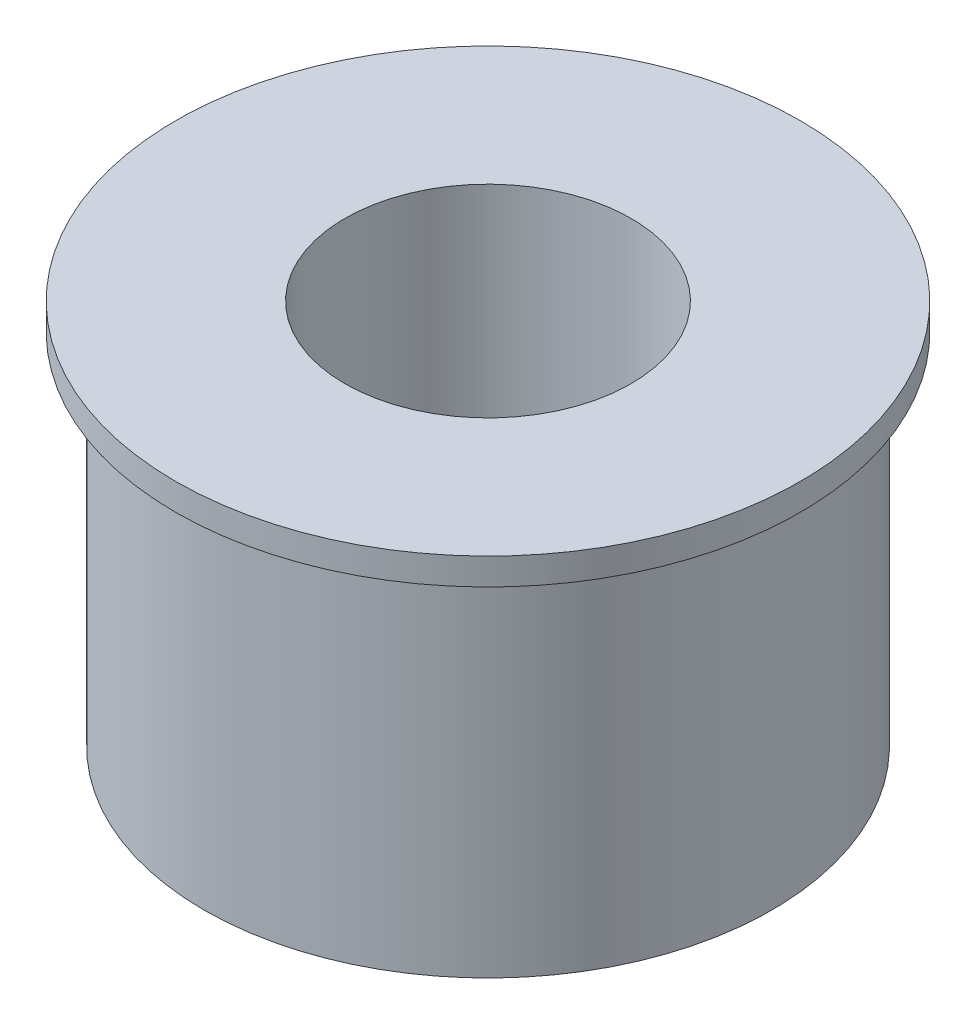
SolidWorks part; units mm, degrees
material "Aluminum Bronze"
ref_plane "Front Plane" through (0, 0, 0) normal (0, 0, 1) x (1, 0, 0)
ref_plane "Top Plane" through (0, 0, 0) normal (0, 1, 0) x (1, 0, 0)
ref_plane "Right Plane" through (0, 0, 0) normal (1, 0, 0) x (0, 0, -1)
sketch "Sketch1" plane through (0, 0, 0) normal (0, 1, 0) x (1, 0, 0)
  circle A0 centre (0, 0) radius 7.95
  circle A1 centre (0, 0) radius 4.01
  dimension "D1" = 8.02
  dimension "D2" = 15.9
extrude "Boss-Extrude1" add sketch "Sketch1" along normal blind 10.8
sketch "Sketch2" plane through (0, 10.8, 0) normal (0, 1, 0) x (-1, 0, 0)
  circle A0 centre (0, 0) radius 5.01
  circle A1 centre (0, 0) radius 8.75
  dimension "D1" = 10.02
  dimension "D2" = 17.5
extrude "Boss-Extrude2" add sketch "Sketch2" against normal blind 0.75
